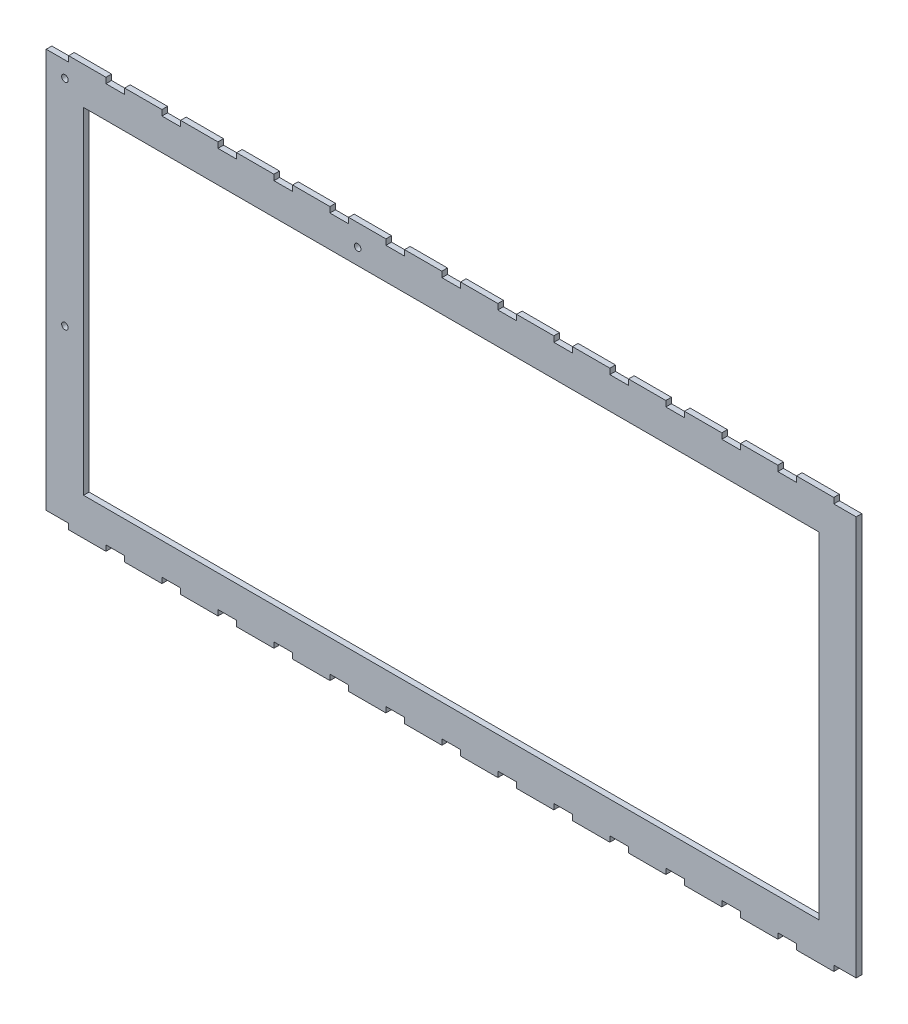
SolidWorks part; units mm, degrees
ref_plane "Plan de face" through (0, 0, 0) normal (0, 0, 1) x (1, 0, 0)
ref_plane "Plan de dessus" through (0, 0, 0) normal (0, 1, 0) x (1, 0, 0)
ref_plane "Plan de droite" through (0, 0, 0) normal (1, 0, 0) x (0, 0, -1)
sketch "Esquisse1" plane through (0, 0, 0) normal (0, 0, 1) x (1, 0, 0)
  line L1 (-217, 110) -> (217, 110)
  line L2 (-217, 110) -> (-217, -110)
  line L3 (-217, -110) -> (217, -110)
  line L4 (217, 110) -> (217, -110)
  line L5 (-217, 110) -> (217, -110) construction
  line L6 (-217, -110) -> (217, 110) construction
  line L11 (-197, 90) -> (197, 90)
  line L12 (-197, 90) -> (-197, -90)
  line L13 (-197, -90) -> (197, -90)
  line L14 (197, 90) -> (197, -90)
  point P0 (0, 0)
  dimension "D1" = 434
  dimension "D2" = 220
  dimension "D3" = 20
  dimension "D4" = 20
  dimension "D5" = 20
  dimension "D6" = 20
extrude "Boss.-Extru.1" add sketch "Esquisse1" along normal blind 3
sketch "Esquisse2" plane through (0, 0, 3) normal (0, 0, 1) x (1, 0, 0)
  line L0 (-217, 0) -> (217, 0) construction
  line L1 (-217, 110) -> (-217, -110) construction
  line L2 (217, -110) -> (217, 110) construction
  line L3 (217, 110) -> (-217, 110) construction
  line L4 (-215, 110) -> (-205, 110)
  line L5 (-215, 110) -> (-215, 107)
  line L6 (-215, 107) -> (-205, 107)
  line L7 (-205, 110) -> (-205, 107)
  line L8 (-185, 110) -> (-185, 107)
  line L9 (-185, 110) -> (-175, 110)
  line L10 (-175, 110) -> (-175, 107)
  line L11 (-185, 107) -> (-175, 107)
  line L12 (-155, 110) -> (-155, 107)
  line L13 (-155, 110) -> (-145, 110)
  line L14 (-145, 110) -> (-145, 107)
  line L15 (-155, 107) -> (-145, 107)
  line L16 (-125, 110) -> (-125, 107)
  line L17 (-125, 110) -> (-115, 110)
  line L18 (-115, 110) -> (-115, 107)
  line L19 (-125, 107) -> (-115, 107)
  line L20 (-95, 110) -> (-95, 107)
  line L21 (-95, 110) -> (-85, 110)
  line L22 (-85, 110) -> (-85, 107)
  line L23 (-95, 107) -> (-85, 107)
  line L24 (-65, 110) -> (-65, 107)
  line L25 (-65, 110) -> (-55, 110)
  line L26 (-55, 110) -> (-55, 107)
  line L27 (-65, 107) -> (-55, 107)
  line L28 (-35, 110) -> (-35, 107)
  line L29 (-35, 110) -> (-25, 110)
  line L30 (-25, 110) -> (-25, 107)
  line L31 (-35, 107) -> (-25, 107)
  line L32 (-5, 110) -> (-5, 107)
  line L33 (-5, 110) -> (5, 110)
  line L34 (5, 110) -> (5, 107)
  line L35 (-5, 107) -> (5, 107)
  line L36 (25, 110) -> (25, 107)
  line L37 (25, 110) -> (35, 110)
  line L38 (35, 110) -> (35, 107)
  line L39 (25, 107) -> (35, 107)
  line L40 (55, 110) -> (55, 107)
  line L41 (55, 110) -> (65, 110)
  line L42 (65, 110) -> (65, 107)
  line L43 (55, 107) -> (65, 107)
  line L44 (85, 110) -> (85, 107)
  line L45 (85, 110) -> (95, 110)
  line L46 (95, 110) -> (95, 107)
  line L47 (85, 107) -> (95, 107)
  line L48 (115, 110) -> (115, 107)
  line L49 (115, 110) -> (125, 110)
  line L50 (125, 110) -> (125, 107)
  line L51 (115, 107) -> (125, 107)
  line L52 (145, 110) -> (145, 107)
  line L53 (145, 110) -> (155, 110)
  line L54 (155, 110) -> (155, 107)
  line L55 (145, 107) -> (155, 107)
  line L56 (175, 110) -> (175, 107)
  line L57 (175, 110) -> (185, 110)
  line L58 (185, 110) -> (185, 107)
  line L59 (175, 107) -> (185, 107)
  line L60 (205, 110) -> (205, 107)
  line L61 (205, 110) -> (215, 110)
  line L62 (215, 110) -> (215, 107)
  line L63 (205, 107) -> (215, 107)
  line L192 (205, -107) -> (215, -107)
  line L193 (215, -110) -> (215, -107)
  line L194 (205, -110) -> (215, -110)
  line L195 (205, -110) -> (205, -107)
  line L196 (175, -107) -> (185, -107)
  line L197 (185, -110) -> (185, -107)
  line L198 (175, -110) -> (185, -110)
  line L199 (175, -110) -> (175, -107)
  line L200 (145, -107) -> (155, -107)
  line L201 (155, -110) -> (155, -107)
  line L202 (145, -110) -> (155, -110)
  line L203 (145, -110) -> (145, -107)
  line L204 (115, -107) -> (125, -107)
  line L205 (125, -110) -> (125, -107)
  line L206 (115, -110) -> (125, -110)
  line L207 (115, -110) -> (115, -107)
  line L208 (85, -107) -> (95, -107)
  line L209 (95, -110) -> (95, -107)
  line L210 (85, -110) -> (95, -110)
  line L211 (85, -110) -> (85, -107)
  line L212 (55, -107) -> (65, -107)
  line L213 (65, -110) -> (65, -107)
  line L214 (55, -110) -> (65, -110)
  line L215 (55, -110) -> (55, -107)
  line L216 (25, -107) -> (35, -107)
  line L217 (35, -110) -> (35, -107)
  line L218 (25, -110) -> (35, -110)
  line L219 (25, -110) -> (25, -107)
  line L220 (-5, -107) -> (5, -107)
  line L221 (5, -110) -> (5, -107)
  line L222 (-5, -110) -> (5, -110)
  line L223 (-5, -110) -> (-5, -107)
  line L224 (-35, -107) -> (-25, -107)
  line L225 (-25, -110) -> (-25, -107)
  line L226 (-35, -110) -> (-25, -110)
  line L227 (-35, -110) -> (-35, -107)
  line L228 (-65, -107) -> (-55, -107)
  line L229 (-55, -110) -> (-55, -107)
  line L230 (-65, -110) -> (-55, -110)
  line L231 (-65, -110) -> (-65, -107)
  line L232 (-95, -107) -> (-85, -107)
  line L233 (-85, -110) -> (-85, -107)
  line L234 (-95, -110) -> (-85, -110)
  line L235 (-95, -110) -> (-95, -107)
  line L236 (-125, -107) -> (-115, -107)
  line L237 (-115, -110) -> (-115, -107)
  line L238 (-125, -110) -> (-115, -110)
  line L239 (-125, -110) -> (-125, -107)
  line L240 (-155, -107) -> (-145, -107)
  line L241 (-145, -110) -> (-145, -107)
  line L242 (-155, -110) -> (-145, -110)
  line L243 (-155, -110) -> (-155, -107)
  line L244 (-185, -107) -> (-175, -107)
  line L245 (-175, -110) -> (-175, -107)
  line L246 (-185, -110) -> (-175, -110)
  line L247 (-185, -110) -> (-185, -107)
  line L248 (-205, -110) -> (-205, -107)
  line L249 (-215, -107) -> (-205, -107)
  line L250 (-215, -110) -> (-215, -107)
  line L251 (-215, -110) -> (-205, -110)
  line L253 (-217, 110) -> (-215, 110)
  line L254 (-217, 110) -> (-217, 107)
  line L255 (-217, 107) -> (-215, 107)
  line L256 (-215, 110) -> (-215, 107)
  line L257 (215, 110) -> (217, 110)
  line L258 (215, 110) -> (215, 107)
  line L259 (215, 107) -> (217, 107)
  line L260 (217, 110) -> (217, 107)
  line L261 (-217, -110) -> (-215, -110)
  line L262 (-217, -110) -> (-217, -107)
  line L263 (-217, -107) -> (-215, -107)
  line L264 (-215, -110) -> (-215, -107)
  line L265 (215, -107) -> (217, -107)
  line L266 (215, -107) -> (215, -110)
  line L267 (215, -110) -> (217, -110)
  line L268 (217, -107) -> (217, -110)
  line M127 (217, 110) -> (-217, 110)
  line M128 (-217, 110) -> (-217, -110)
  line M129 (-217, -110) -> (217, -110)
  dimension "D1" = 3
  dimension "D2" = 10
  dimension "D3" = 2
  dimension "D5" = 20
  dimension "D4" = 15
extrude "Enlèv. mat.-Extru.1" cut sketch "Esquisse2" against normal blind 3 contours L7 L5 L6 M127 | L8 L11 L10 M127 | L12 L15 L14 M127 | L16 L19 L18 M127 | L20 L23 L22 M127 | L28 L31 L30 M127 | L36 L39 L38 M127 | L40 L43 L42 M127 | L44 L47 L46 M127 | L48 L51 L50 M127 | L52 L55 L54 M127 | L56 L59 L58 M127 | L60 L63 L62 M127 | L195 L193 L192 M129 | L199 L197 L196 M129 | L203 L201 L200 M129 | L211 L209 L208 M129 | L215 L213 L212 M129 | L227 L225 L224 M129 | L231 L229 L228 M129 | L235 L233 L232 M129 | L239 L237 L236 M129 | L243 L241 L240 M129 | L250 L248 L249 M129 | L247 L245 L244 M129 | L263 L250 M128 M129 | L255 L5 M128 M127 | L25 L26 L27 L24 | L33 L34 L35 L32 | L204 L205 L206 L207 | L216 L217 L218 L219 | L220 L221 L222 L223 | L258 L257 L260 L259 | L266 L265 L268 L267
sketch "Esquisse3" plane through (0, 0, 3) normal (0, 0, 1) x (1, 0, 0)
  line L0 (-217, 107) -> (-197, 90) construction
  line L1 (-207, 98.5) -> (-50.1, 98.5) construction
  line L2 (-207, 98.5) -> (-207, -16.46) construction
  circle A0 centre (-207, 98.5) radius 1.75
  circle A1 centre (-50.1, 98.5) radius 1.75
  circle A2 centre (-207, -16.46) radius 1.75
  dimension "D1" = 3.5
  dimension "D4" = 3.5
  dimension "D5" = 3.5
  dimension "D2" = 114.96
  dimension "D3" = 156.9
extrude "Enlèv. mat.-Extru.2" cut sketch "Esquisse3" against normal blind 3
